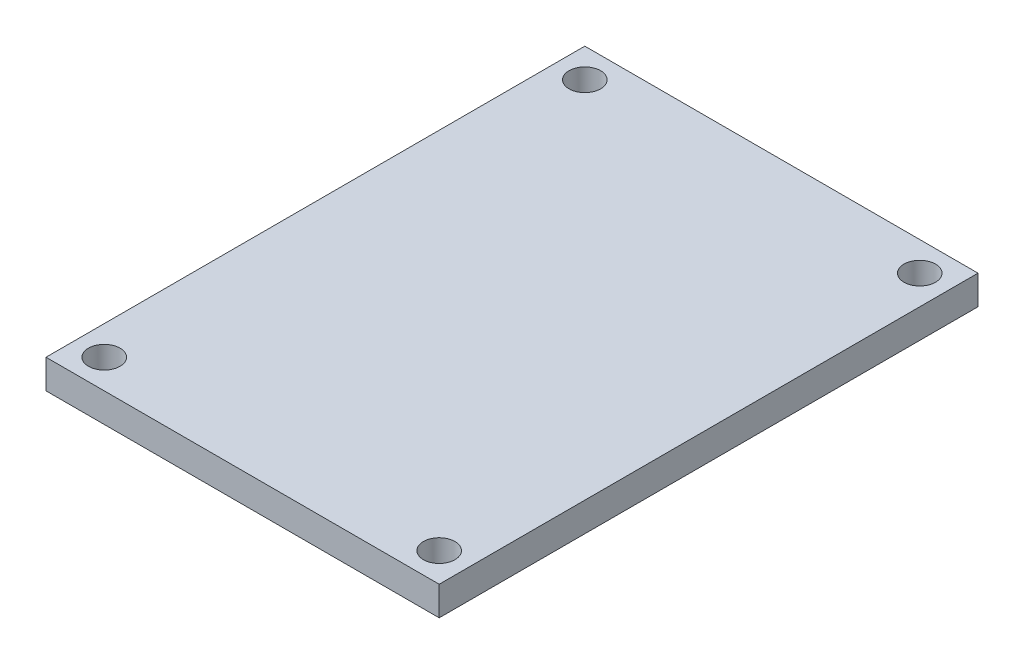
SolidWorks part; units mm, degrees
ref_plane "Front Plane" through (0, 0, 0) normal (0, 0, 1) x (1, 0, 0)
ref_plane "Top Plane" through (0, 0, 0) normal (0, 1, 0) x (1, 0, 0)
ref_plane "Right Plane" through (0, 0, 0) normal (1, 0, 0) x (0, 0, -1)
sketch "Sketch1" plane through (0, 0, 0) normal (0, 1, 0) x (1, 0, 0)
  line L1 (-20.25, -27.75) -> (20.25, -27.75)
  line L2 (-20.25, -27.75) -> (-20.25, 27.75)
  line L3 (-20.25, 27.75) -> (20.25, 27.75)
  line L4 (20.25, -27.75) -> (20.25, 27.75)
  line L5 (-20.25, -27.75) -> (20.25, 27.75) construction
  line L6 (-20.25, 27.75) -> (20.25, -27.75) construction
  point P0 (0, 0)
  dimension "D1" = 40.5
  dimension "D2" = 55.5
extrude "Boss-Extrude1" add sketch "Sketch1" along normal blind 3
sketch "Sketch2" plane through (0, 3, 0) normal (0, 1, 0) x (1, 0, 0)
  line L0 (-1002.1798, 24.75) -> (48997.8202, 24.75) construction
  line L1 (-999.564, -24.75) -> (49000.436, -24.75) construction
  line L2 (-17.25, -1002.5432) -> (-17.25, 48997.4568) construction
  line L3 (17.25, -1005.0863) -> (17.25, 48994.9137) construction
  line L4 (-20.25, 27.75) -> (-20.25, -27.75) construction
  line L5 (20.25, 27.75) -> (-20.25, 27.75) construction
  line L6 (20.25, -27.75) -> (20.25, 27.75) construction
  line L7 (-20.25, -27.75) -> (20.25, -27.75) construction
  circle A0 centre (-17.25, 24.75) radius 1.625
  circle A1 centre (17.25, 24.75) radius 1.625
  circle A2 centre (17.25, -24.75) radius 1.625
  circle A3 centre (-17.25, -24.75) radius 1.625
  dimension "D6" = 3.25
  dimension "D8" = 3.25
  dimension "D10" = 3.25
  dimension "D12" = 3.25
  dimension "D1" = 3
  dimension "D2" = 3
  dimension "D3" = 3
  dimension "D4" = 3
  dimension "D5" = 0
  dimension "D7" = 0
  dimension "D9" = 0
  dimension "D11" = 0
extrude "Cut-Extrude1" cut sketch "Sketch2" against normal through all both and the other way through all
